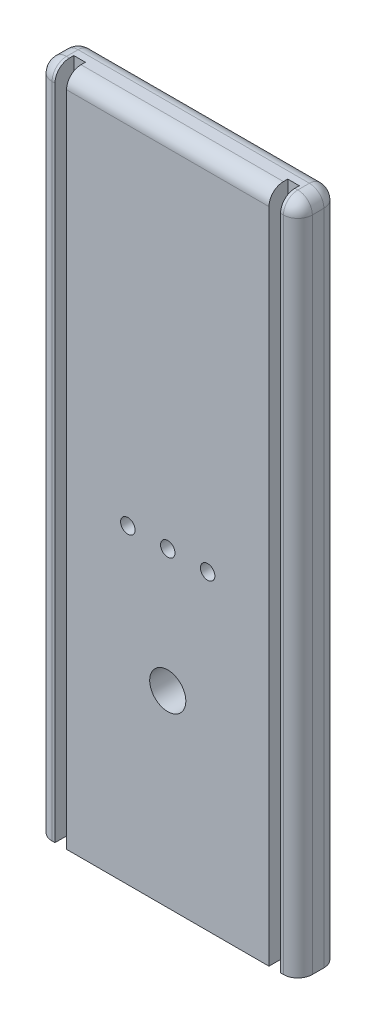
SolidWorks part; units mm, degrees
material "Oak"
ref_plane "Front Plane" through (0, 0, 0) normal (0, 0, 1) x (1, 0, 0)
ref_plane "Top Plane" through (0, 0, 0) normal (0, 1, 0) x (1, 0, 0)
ref_plane "Right Plane" through (0, 0, 0) normal (1, 0, 0) x (0, 0, -1)
sketch "Sketch1" plane through (0, 0, 0) normal (0, 0, 1) x (1, 0, 0)
  line L1 (-57.15, -147.6375) -> (57.15, -147.6375)
  line L2 (-57.15, -147.6375) -> (-57.15, 147.6375)
  line L3 (-57.15, 147.6375) -> (57.15, 147.6375)
  line L4 (57.15, -147.6375) -> (57.15, 147.6375)
  line L5 (-57.15, -147.6375) -> (57.15, 147.6375) construction
  line L6 (-57.15, 147.6375) -> (57.15, -147.6375) construction
  point P0 (0, 0)
  dimension "D1" = 114.3
  dimension "D2" = 295.275
extrude "Boss-Extrude1" add sketch "Sketch1" along normal mid plane 17.78
sketch "Sketch2" plane through (0, 0, 8.89) normal (0, 0, 1) x (1, 0, 0)
  line L0 (57.15, 147.6375) -> (-57.15, 147.6375) construction
  circle A0 centre (0, -11.1125) radius 3.175
  circle A1 centre (-17.526, -11.1125) radius 3.175
  circle A2 centre (17.526, -11.1125) radius 3.175
  dimension "D1" = 6.35
  dimension "D2" = 158.75
  dimension "D3" = 17.526
  dimension "D4" = 17.526
extrude "Cut-Extrude1" cut sketch "Sketch2" against normal blind 12.7
sketch "Sketch3" plane through (0, 147.6375, 0) normal (0, 1, 0) x (1, 0, 0)
  line L0 (57.15, -8.89) -> (-57.15, -8.89) construction
  line L1 (-49.53, -8.89) -> (-44.45, -8.89)
  line L2 (-49.53, -8.89) -> (-49.53, -0.635)
  line L3 (-49.53, -0.635) -> (-44.45, -0.635)
  line L4 (-44.45, -8.89) -> (-44.45, -0.635)
  dimension "D1" = 5.08
  dimension "D2" = 8.255
  dimension "D3" = 44.45
extrude "Cut-Extrude2" cut sketch "Sketch3" against normal through all
mirror "Mirror1" about plane through (0, 0, 0) normal (1, 0, 0) of "Cut-Extrude2"
sketch "Sketch4" plane through (0, 0, -8.89) normal (0, 0, -1) x (-1, 0, 0)
  line L0 (57.15, -147.6375) -> (-57.15, -147.6375) construction
  line L1 (-31.75, -52.3875) -> (31.75, -52.3875)
  line L2 (-31.75, -52.3875) -> (-31.75, -71.4375)
  line L3 (-31.75, -71.4375) -> (31.75, -71.4375)
  line L4 (31.75, -52.3875) -> (31.75, -71.4375)
  line L5 (-31.75, -52.3875) -> (31.75, -71.4375) construction
  line L6 (-31.75, -71.4375) -> (31.75, -52.3875) construction
  line L7 (-57.15, -147.6375) -> (-57.15, 147.6375) construction
  line L8 (57.15, 147.6375) -> (57.15, -147.6375) construction
  point P0 (0, -61.9125)
  dimension "D1" = 76.2
  dimension "D2" = 19.05
  dimension "D3" = 25.4
  dimension "D4" = 25.4
extrude "Cut-Extrude3" [suppressed] cut sketch "Sketch4" against normal through all
fillet "Fillet1" radius 6.35 10 edges at (57.15, 0, -8.89) (0, 147.6375, -8.89) (57.15, 0, 8.89) (-53.34, 147.6375, 8.89) (0, 147.6375, 8.89) (53.34, 147.6375, 8.89) (-57.15, 147.6375, 0) (57.15, 147.6375, 0) (-57.15, 0, -8.89) (-57.15, 0, 8.89)
sketch "Sketch5" plane through (0, 0, 8.89) normal (0, 0, 1) x (1, 0, 0)
  line L0 (-44.45, -147.6375) -> (44.45, -147.6375) construction
  line L1 (57.15, 141.2875) -> (57.15, -147.6375) construction
  circle A0 centre (0, -65.0875) radius 7.9375
  dimension "D1" = 15.875
  dimension "D2" = 82.55
  dimension "D3" = 57.15
extrude "Cut-Extrude4" cut sketch "Sketch5" against normal through all
chamfer "Chamfer1" [suppressed] distance 12.7 distance2 19.05
chamfer "Chamfer2" [suppressed] distance 19.05 angle 30
equation "\".70.10in\"=0.1"
